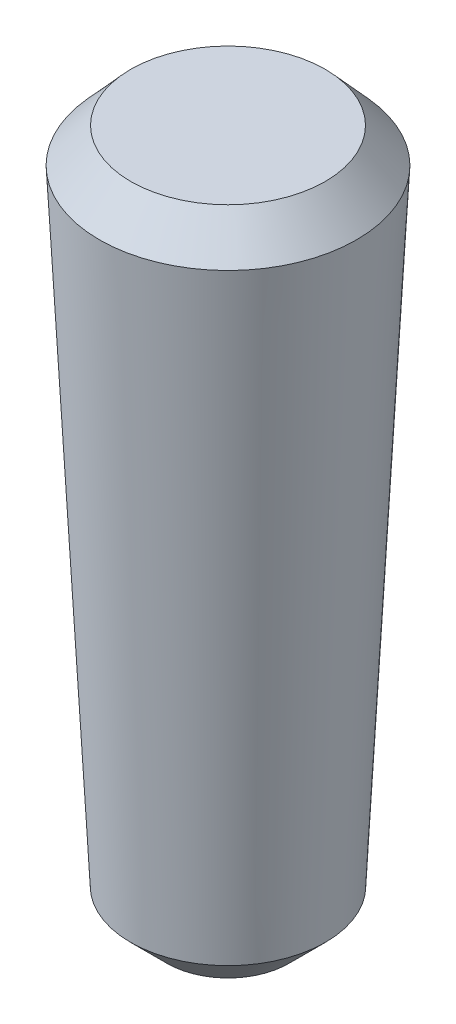
SolidWorks part; units mm, degrees
ref_plane "Front Plane" through (0, 0, 0) normal (0, 0, 1) x (1, 0, 0)
ref_plane "Top Plane" through (0, 0, 0) normal (0, 1, 0) x (1, 0, 0)
ref_plane "Right Plane" through (0, 0, 0) normal (1, 0, 0) x (0, 0, -1)
sketch "Sketch1" plane through (0, 0, 0) normal (0, 1, 0) x (1, 0, 0)
  circle A0 centre (0, 0) radius 1.375
  dimension "D1" = 2.75
ref_plane "Plane1" through (0, 10, 0) normal (0, 1, 0) x (1, 0, 0)
sketch "Sketch2" plane through (0, 10, 0) normal (0, 1, 0) x (1, 0, 0)
  circle A0 centre (0, 0) radius 1.875
  dimension "D1" = 3.75
loft "Loft1" add profiles "Sketch2", "Sketch1"
chamfer "Chamfer1" distance 0.5 angle 45 2 edges at (0, 0, 1.375) (0, 10, 1.875)
